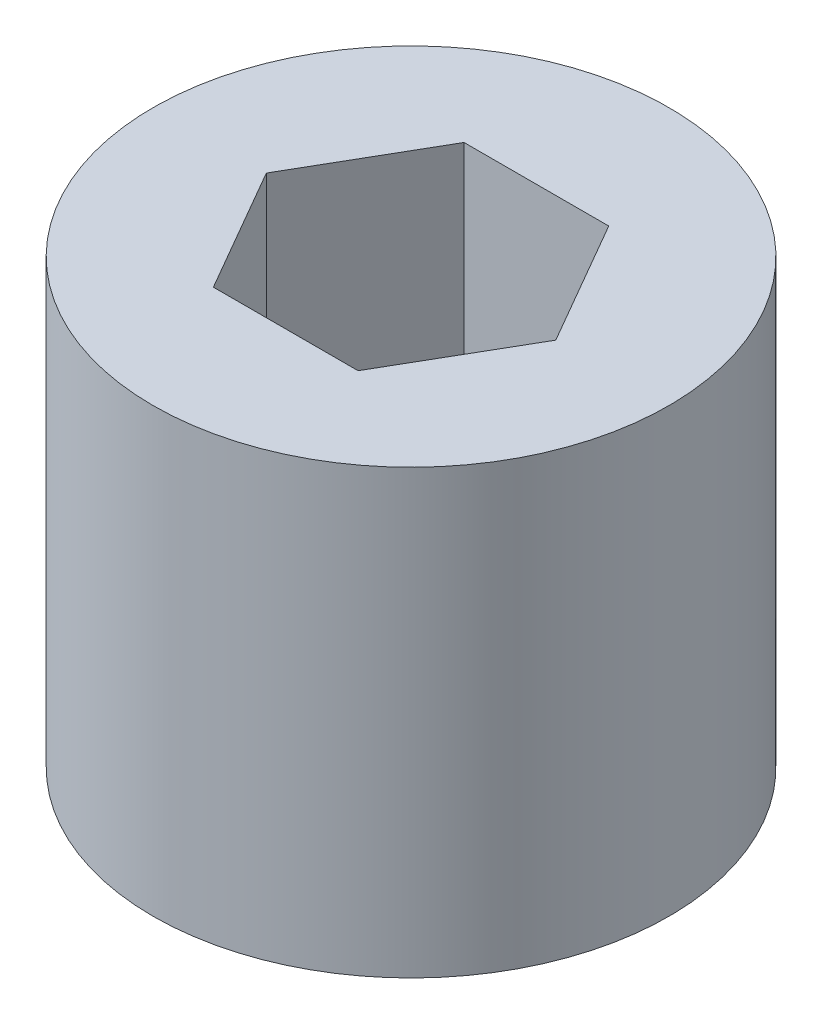
SolidWorks part; units mm, degrees
ref_plane "Front Plane" through (0, 0, 0) normal (0, 0, 1) x (1, 0, 0)
ref_plane "Top Plane" through (0, 0, 0) normal (0, 1, 0) x (1, 0, 0)
ref_plane "Right Plane" through (0, 0, 0) normal (1, 0, 0) x (0, 0, -1)
sketch "Sketch1" plane through (0, 0, 0) normal (0, 1, 0) x (1, 0, 0)
  line L1 (4.9075, 0) -> (2.4537, 4.25)
  line L2 (2.4537, 4.25) -> (-2.4537, 4.25)
  line L3 (-2.4537, 4.25) -> (-4.9075, 0)
  line L4 (-4.9075, 0) -> (-2.4537, -4.25)
  line L5 (-2.4537, -4.25) -> (2.4537, -4.25)
  line L6 (2.4537, -4.25) -> (4.9075, 0)
  circle A0 centre (0, 0) radius 4.25 construction
  circle A1 centre (0, 0) radius 8.75
  dimension "D2" = 17.5
  dimension "D1" = 8.5
extrude "Boss-Extrude1" add sketch "Sketch1" along normal blind 15
